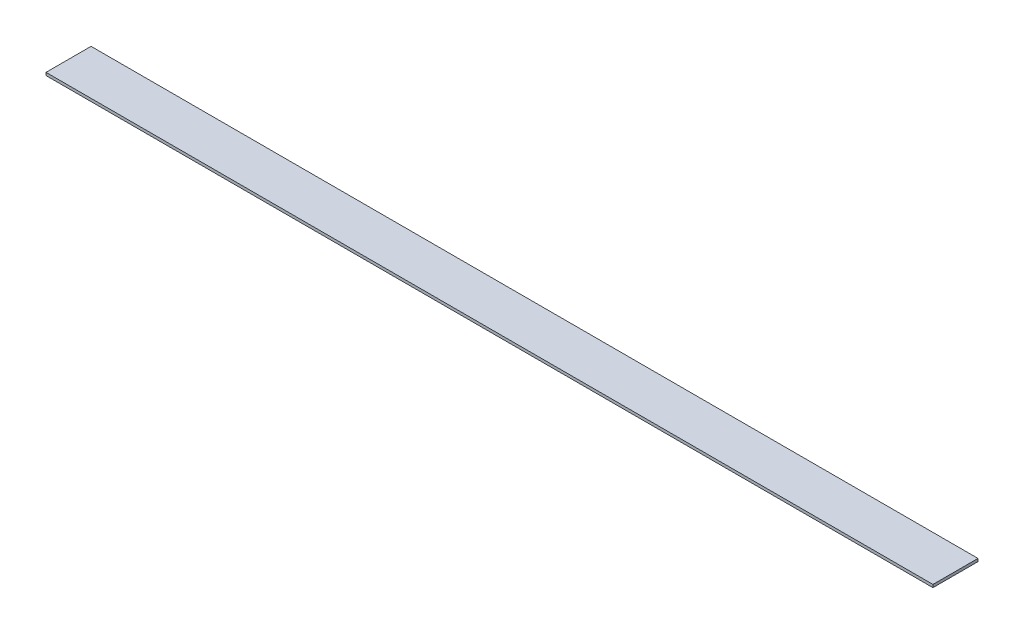
SolidWorks part; units mm, degrees
material "Aleación 1060"
ref_plane "Front Plane" through (0, 0, 0) normal (0, 0, 1) x (1, 0, 0)
ref_plane "Top Plane" through (0, 0, 0) normal (0, 1, 0) x (1, 0, 0)
ref_plane "Right Plane" through (0, 0, 0) normal (1, 0, 0) x (0, 0, -1)
sketch "Croquis1" plane through (0, 0, 0) normal (1, 0, 0) x (0, 0, -1)
  line L1 (25.4, -1.5875) -> (-25.4, -1.5875)
  line L2 (25.4, -1.5875) -> (25.4, 1.5875)
  line L3 (25.4, 1.5875) -> (-25.4, 1.5875)
  line L4 (-25.4, -1.5875) -> (-25.4, 1.5875)
  line L5 (25.4, -1.5875) -> (-25.4, 1.5875) construction
  line L6 (25.4, 1.5875) -> (-25.4, -1.5875) construction
  point P0 (0, 0)
  dimension "D1" = 50.8
  dimension "D2" = 3.175
extrude "Saliente-Extruir1" add sketch "Croquis1" against normal blind 1000
equation "\"D1@Croquis1\"=2*25.4"
